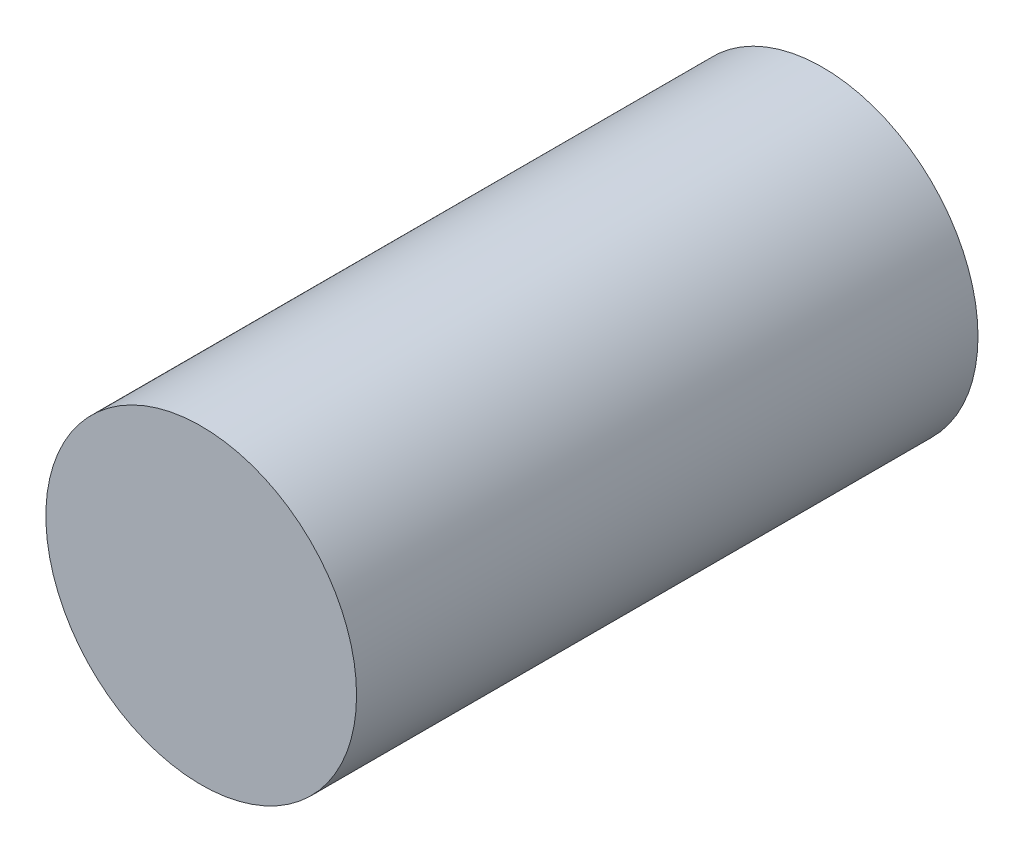
SolidWorks part; units mm, degrees
ref_plane "Plano frontal" through (0, 0, 0) normal (0, 0, 1) x (1, 0, 0)
ref_plane "Plano superior" through (0, 0, 0) normal (0, 1, 0) x (1, 0, 0)
ref_plane "Plano direito" through (0, 0, 0) normal (1, 0, 0) x (0, 0, -1)
sketch "Esboço1" plane through (0, 0, 0) normal (0, 0, 1) x (1, 0, 0)
  circle A0 centre (0, 0) radius 2.5
  dimension "D1" = 5
extrude "Ressalto-extrusão1" add sketch "Esboço1" along normal blind 10
